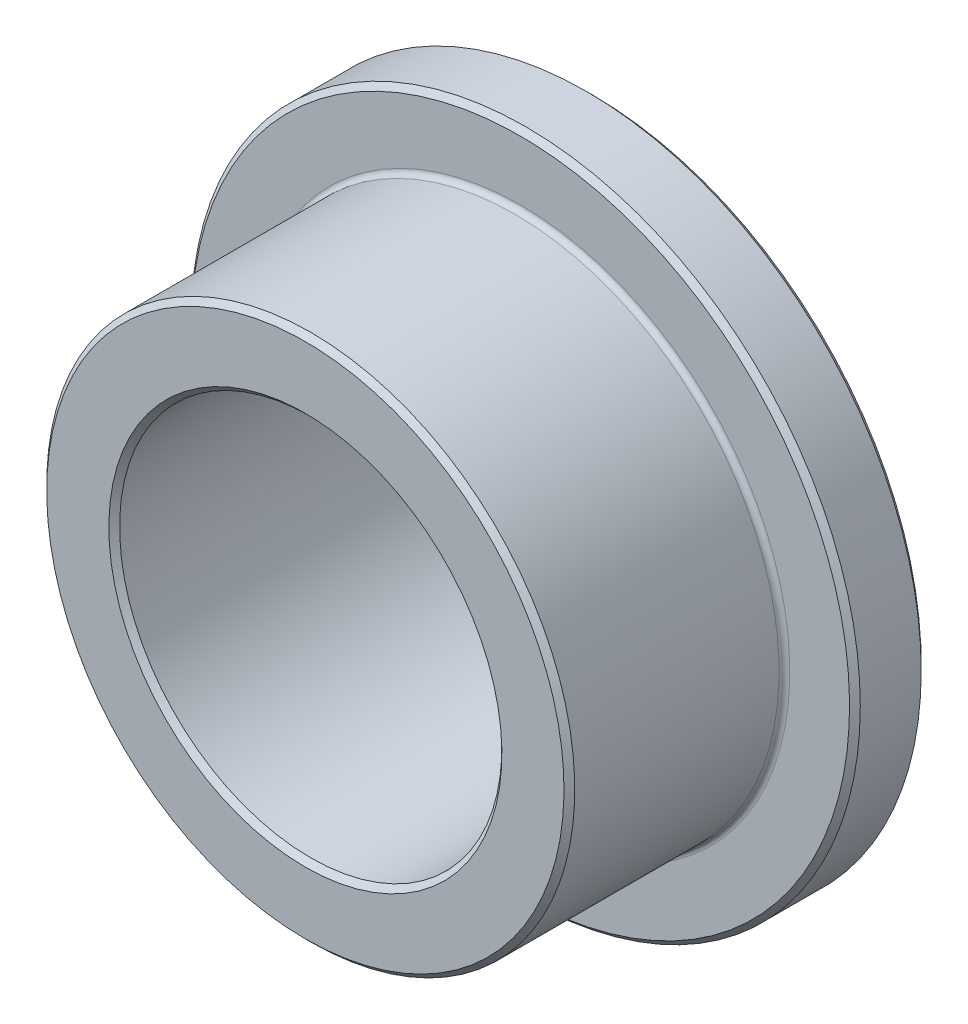
SolidWorks part; units mm, degrees
ref_plane "Front Plane" through (0, 0, 0) normal (0, 0, 1) x (1, 0, 0)
ref_plane "Top Plane" through (0, 0, 0) normal (0, 1, 0) x (1, 0, 0)
ref_plane "Right Plane" through (0, 0, 0) normal (1, 0, 0) x (0, 0, -1)
sketch "Sketch1" plane through (0, 0, 0) normal (0, 0, 1) x (1, 0, 0)
  circle A0 centre (0, 0) radius 4
  circle A1 centre (0, 0) radius 5.525
  circle A2 centre (0, 0) radius 7
  point P5 (0, 5.525)
  point P6 (0, 4)
  point P7 (0, 7)
  dimension "ID" = 8
  dimension "OD" = 11.05
  dimension "Flange OD" = 14
sketch "Sketch2" plane through (0, 0, 0) normal (1, 0, 0) x (0, 0, -1)
  line L0 (3, 0) -> (-3, 0)
  line L1 (3, 0) -> (3, 7)
  line L2 (3, 7) -> (1.5, 7)
  line L3 (1.5, 7) -> (1.5, 5.525)
  line L4 (1.5, 5.525) -> (-3, 5.525)
  line L5 (-3, 5.525) -> (-3, 4)
  line L6 (-3, 4) -> (3, 4)
  point P4 (0, 0)
  dimension "Flange Thickness" = 1.5
  dimension "Length" = 6
sketch "Sketch3" plane through (0, 0, 0) normal (1, 0, 0) x (0, 0, -1)
  line L0 (3, 7) -> (1.5, 7) construction
  line L1 (1.5, 7) -> (1.5, 5.525) construction
  line L2 (1.5, 5.525) -> (-3, 5.525) construction
  line L3 (-3, 4) -> (3, 4) construction
  line L4 (-3, 5.525) -> (-3, 4) construction
  line L5 (3, 7) -> (1.5, 7)
  line L6 (1.5, 7) -> (1.5, 5.525)
  line L7 (1.5, 5.525) -> (-3, 5.525)
  line L8 (-3, 4) -> (3, 4)
  line L9 (-3, 5.525) -> (-3, 4)
  line L10 (3, 7) -> (3, 4)
revolve "Revolve1" add sketch "Sketch3" angle 360 about L0
chamfer "Chamfer1" distance 0.1125 angle 45 4 edges at (0, 7, -3) (0, 7, -1.5) (0, 5.525, 3) (0, 4, 3)
fillet "Fillet1" radius 0.1125 1 edges at (0, 5.525, -1.5)
equation "\"D1@Chamfer1\"=\"Flange Thickness@Sketch2\"*.075"
equation "\"D1@Fillet1\"=\"D1@Chamfer1\""
